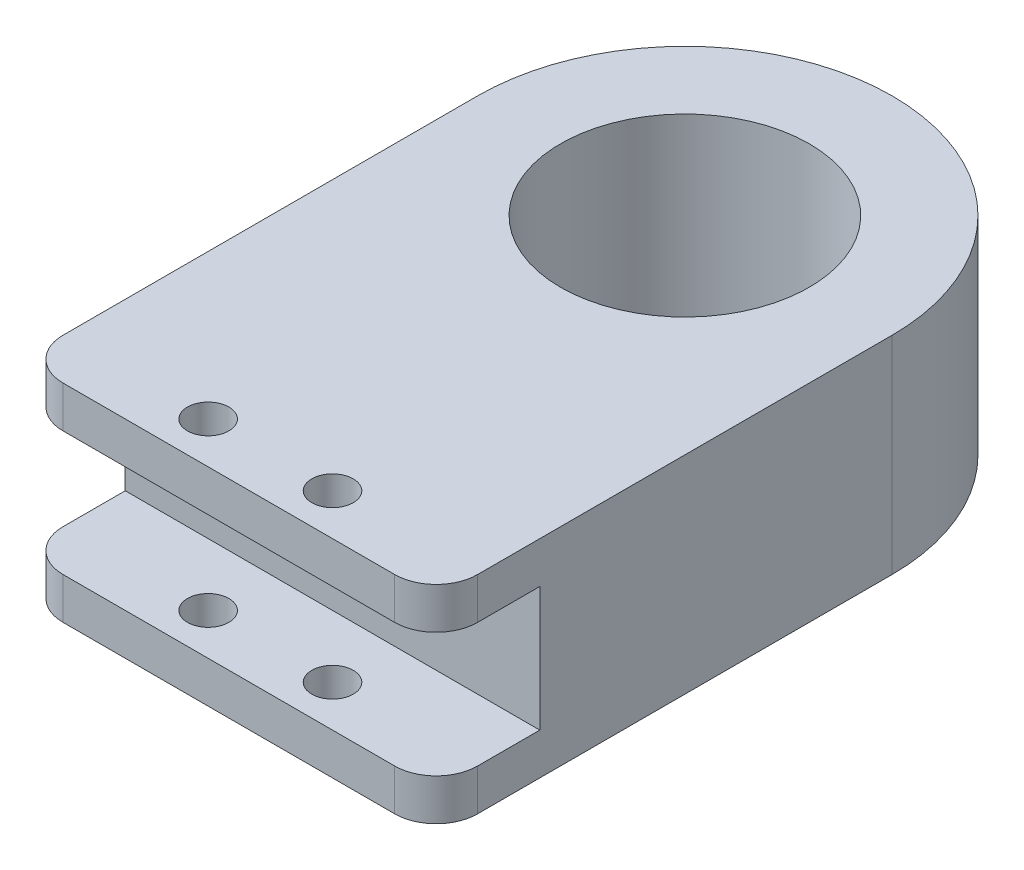
SolidWorks part; units mm, degrees
ref_plane "Front Plane" through (0, 0, 0) normal (0, 0, 1) x (1, 0, 0)
ref_plane "Top Plane" through (0, 0, 0) normal (0, 1, 0) x (1, 0, 0)
ref_plane "Right Plane" through (0, 0, 0) normal (1, 0, 0) x (0, 0, -1)
sketch "Sketch1" plane through (0, 0, 0) normal (0, 1, 0) x (1, 0, 0)
  line L0 (0, 152.8942) -> (0, -188.4323) construction
  line L1 (50, -85) -> (263.3425, -85) construction
  line L2 (263.3425, 0) -> (-283.0233, 0) construction
  line L3 (-265.9874, -110) -> (263.3425, -110) construction
  line L4 (-50, -60) -> (-50, 0)
  line L6 (50, -60) -> (50, -100)
  line L7 (40, -110) -> (-40, -110)
  line L8 (-50, -60) -> (-50, -100)
  line L10 (50, -110) -> (0, -85) construction
  line L11 (50, -60) -> (50, 0)
  circle A1 centre (0, 0) radius 30
  arc A2 (50, 0) -> (-50, 0) centre (0, 0) ccw
  arc A3 (50, -100) -> (40, -110) centre (40, -100) cw
  arc A4 (-40, -110) -> (-50, -100) centre (-40, -100) cw
  circle A5 centre (-15, -100) radius 5
  circle A6 centre (15, -100) radius 5
  point P24 (-50, -110)
  dimension "D1" = 85
  dimension "D2" = 60
  dimension "D4" = 10
  dimension "D5" = 10
  dimension "D3" = 25
  dimension "D6" = 15
  dimension "D7" = 10
extrude "Boss-Extrude1" add sketch "Sketch1" along normal blind 50
sketch "Sketch2" plane through (50, 0, 0) normal (1, 0, 0) x (0, 0, -1)
  line L0 (-110, 50) -> (-110, 0) construction
  line L1 (-110, 40) -> (-85, 40)
  line L2 (-110, 40) -> (-110, 10)
  line L3 (-110, 10) -> (-85, 10)
  line L4 (-85, 40) -> (-85, 10)
  line L5 (-100, 50) -> (0, 50) construction
  dimension "D1" = 30
  dimension "D2" = 25
  dimension "D3" = 10
extrude "Cut-Extrude1" cut sketch "Sketch2" against normal through all
